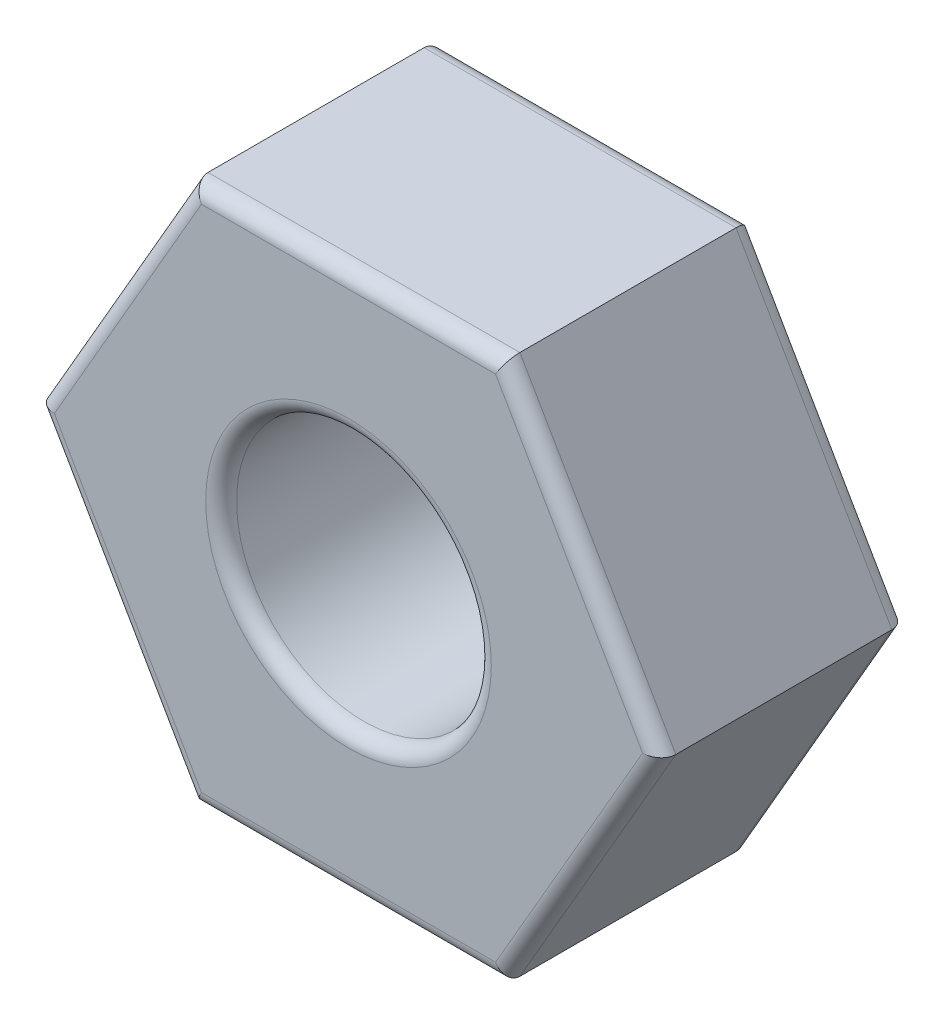
SolidWorks part; units mm, degrees
ref_plane "Front Plane" through (0, 0, 0) normal (0, 0, 1) x (1, 0, 0)
ref_plane "Top Plane" through (0, 0, 0) normal (0, 1, 0) x (1, 0, 0)
ref_plane "Right Plane" through (0, 0, 0) normal (1, 0, 0) x (0, 0, -1)
sketch "Sketch1" plane through (0, 0, 0) normal (0, 0, 1) x (1, 0, 0)
  line L1 (4.0415, 0) -> (2.0207, 3.5)
  line L2 (2.0207, 3.5) -> (-2.0207, 3.5)
  line L3 (-2.0207, 3.5) -> (-4.0415, 0)
  line L4 (-4.0415, 0) -> (-2.0207, -3.5)
  line L5 (-2.0207, -3.5) -> (2.0207, -3.5)
  line L6 (2.0207, -3.5) -> (4.0415, 0)
  circle A0 centre (0, 0) radius 3.5 construction
  circle A1 centre (0, 0) radius 1.65
  dimension "D1" = 7
  dimension "D2" = 3.3
extrude "Boss-Extrude1" add sketch "Sketch1" along normal blind 3.2
fillet "Fillet1" radius 0.2 14 edges at (1.65, 0, 3.2) (0, -3.5, 3.2) (-3.0311, -1.75, 3.2) (-3.0311, 1.75, 3.2) (0, 3.5, 3.2) (3.0311, 1.75, 3.2) (3.0311, -1.75, 3.2) (1.65, 0, 0) (3.0311, 1.75, 0) (0, 3.5, 0) (-3.0311, 1.75, 0) (-3.0311, -1.75, 0) (0, -3.5, 0) (3.0311, -1.75, 0)
